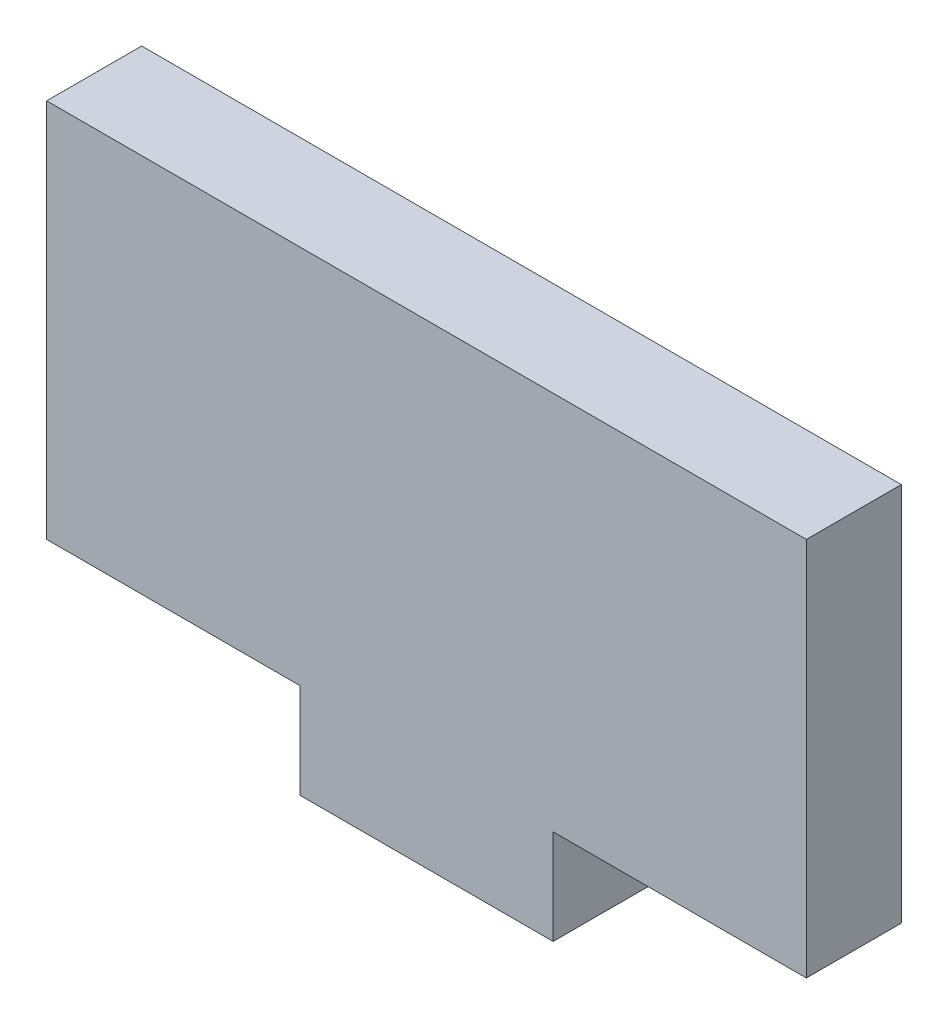
SolidWorks part; units mm, degrees
ref_plane "Front Plane" through (0, 0, 0) normal (0, 0, 1) x (1, 0, 0)
ref_plane "Top Plane" through (0, 0, 0) normal (0, 1, 0) x (1, 0, 0)
ref_plane "Right Plane" through (0, 0, 0) normal (1, 0, 0) x (0, 0, -1)
sketch "Sketch1" plane through (0, 0, 0) normal (0, 0, 1) x (1, 0, 0)
  line L0 (33.8667, 0) -> (50.8, 0)
  line L1 (0, 0) -> (16.9333, 0)
  line L2 (0, 0) -> (0, 25.4)
  line L3 (0, 25.4) -> (50.8, 25.4)
  line L4 (50.8, 0) -> (50.8, 25.4)
  line L6 (16.9333, 0) -> (16.9333, -6.35)
  line L7 (16.9333, -6.35) -> (33.8667, -6.35)
  line L8 (33.8667, 0) -> (33.8667, -6.35)
  dimension "D1" = 50.8
  dimension "D2" = 25.4
  dimension "D3" = 6.35
extrude "Boss-Extrude1" add sketch "Sketch1" along normal blind 6.35
equation "\"mat\"= \"mat@jaws.assembly\""
equation "\"D3@Sketch1\"= \"mat\""
equation "\"D1@Boss-Extrude1\"= \"mat\""
